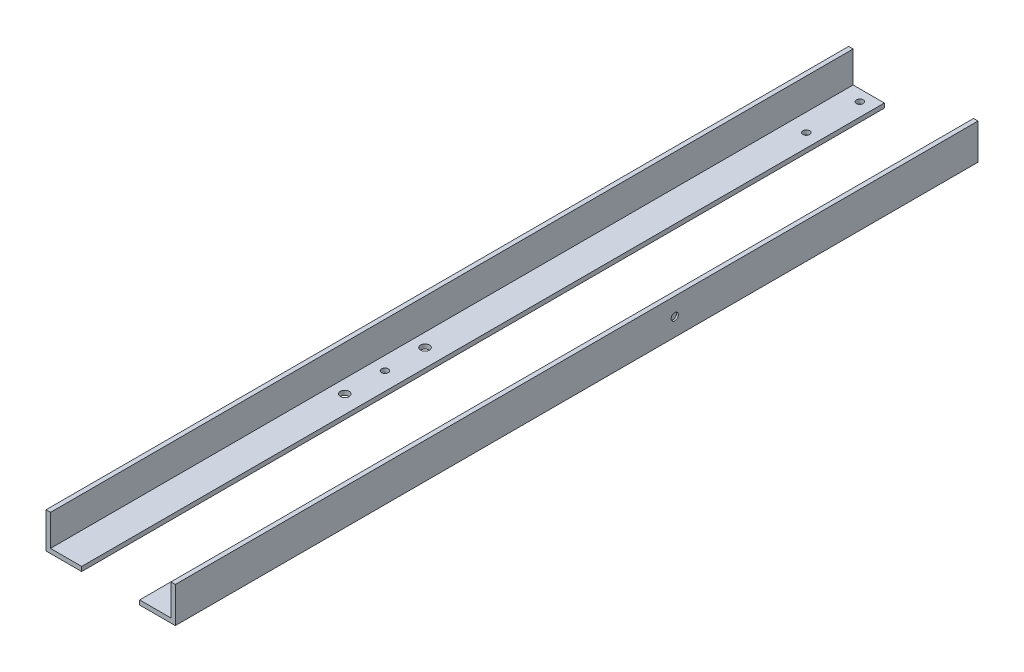
SolidWorks part; units mm, degrees
ref_plane "Front Plane" through (0, 0, 0) normal (0, 0, 1) x (1, 0, 0)
ref_plane "Top Plane" through (0, 0, 0) normal (0, 1, 0) x (1, 0, 0)
ref_plane "Right Plane" through (0, 0, 0) normal (1, 0, 0) x (0, 0, -1)
sketch "Sketch1" plane through (0, 0, 0) normal (0, 1, 0) x (1, 0, 0)
  line L1 (-92.075, -571.5) -> (92.075, -571.5)
  line L2 (-92.075, -571.5) -> (-92.075, 571.5)
  line L3 (-92.075, 571.5) -> (92.075, 571.5)
  line L4 (92.075, -571.5) -> (92.075, 571.5)
  line L5 (-92.075, -571.5) -> (92.075, 571.5) construction
  line L6 (-92.075, 571.5) -> (92.075, -571.5) construction
  point P0 (0, 0)
  dimension "D1" = 1143
  dimension "D2" = 184.15
extrude "Boss-Extrude1" add sketch "Sketch1" along normal blind 50.8
sketch "Sketch2" plane through (0, 0, 571.5) normal (0, 0, 1) x (1, 0, 0)
  line L0 (-92.075, 50.8) -> (92.075, 50.8) construction
  line L1 (-85.725, 50.8) -> (85.725, 50.8)
  line L2 (-85.725, 50.8) -> (-85.725, 6.35)
  line L3 (-85.725, 6.35) -> (-41.275, 6.35)
  line L4 (85.725, 50.8) -> (85.725, 6.35)
  line L5 (-92.075, 50.8) -> (-92.075, 0) construction
  line L6 (92.075, 50.8) -> (92.075, 0) construction
  line L7 (-92.075, 0) -> (92.075, 0) construction
  line L9 (-41.275, 6.35) -> (-41.275, 0)
  line L10 (-41.275, 0) -> (41.275, 0)
  line L11 (41.275, 6.35) -> (41.275, 0)
  line L12 (41.275, 6.35) -> (85.725, 6.35)
  point P16 (-41.275, 3.175)
  dimension "D1" = 6.35
  dimension "D2" = 6.35
  dimension "D3" = 44.45
  dimension "D4" = 50.8
  dimension "D5" = 50.8
extrude "Cut-Extrude1" cut sketch "Sketch2" against normal through all
sketch "Sketch3" plane through (0, 6.35, 0) normal (0, 1, 0) x (1, 0, 0)
  line L0 (-85.725, 571.5) -> (-41.275, 571.5) construction
  line L2 (-41.275, 571.5) -> (-41.275, -571.5) construction
  line L3 (-85.725, -571.5) -> (-41.275, -571.5) construction
  line L4 (41.275, 571.5) -> (41.275, -571.5) construction
  circle A0 centre (-60.325, 555.625) radius 4.7625
  circle A1 centre (-60.325, 479.425) radius 4.7625
  circle A2 centre (-66.675, -114.3) radius 4.7625
  circle A3 centre (60.325, 555.625) radius 4.7625
  circle A4 centre (60.325, 479.425) radius 4.7625
  circle A6 centre (60.325, -114.3) radius 4.7625
  circle A7 centre (-66.675, -57.15) radius 6.35
  circle A8 centre (-66.675, -171.45) radius 6.35
  circle A9 centre (60.325, -57.15) radius 6.35
  circle A10 centre (60.325, -171.45) radius 6.35
  dimension "D6" = 9.525
  dimension "D7" = 9.525
  dimension "D8" = 9.525
  dimension "D10" = 9.525
  dimension "D11" = 9.525
  dimension "D12" = 9.525
  dimension "D13" = 12.7
  dimension "D14" = 12.7
  dimension "D17" = 12.7
  dimension "D18" = 12.7
  dimension "D1" = 15.875
  dimension "D2" = 19.05
  dimension "D3" = 92.075
  dimension "D4" = 25.4
  dimension "D5" = 457.2
  dimension "D9" = 19.05
  dimension "D15" = 57.15
  dimension "D16" = 57.15
  dimension "D19" = 57.15
  dimension "D20" = 0
  dimension "D21" = 57.15
extrude "Bolt Hole Cuts" cut sketch "Sketch3" against normal through all
sketch "Sketch4" plane through (92.075, 0, 0) normal (1, 0, 0) x (0, 0, -1)
  line L0 (571.5, 50.8) -> (571.5, 0) construction
  line L1 (-571.5, 50.8) -> (571.5, 50.8) construction
  circle A0 centre (139.7, 25.4) radius 5.1308
  dimension "D1" = 10.2616
  dimension "D2" = 431.8
  dimension "D3" = 25.4
extrude "Cut-Extrude2" cut sketch "Sketch4" against normal blind 2.54
